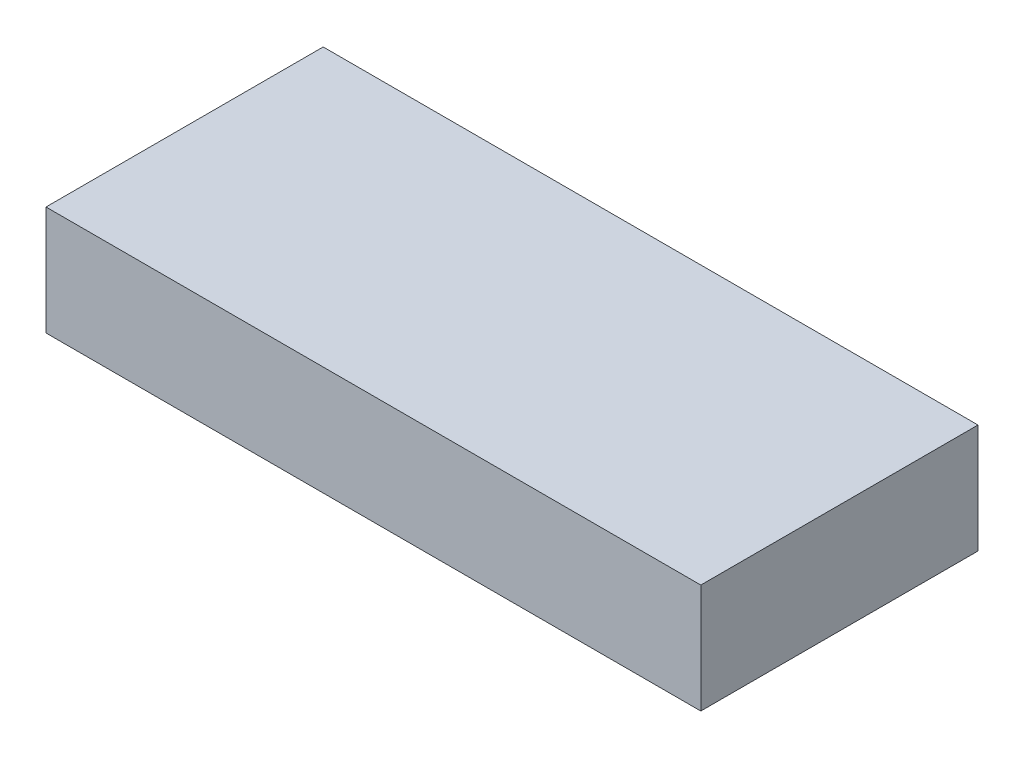
SolidWorks part; units mm, degrees
ref_plane "Front Plane" through (0, 0, 0) normal (0, 0, 1) x (1, 0, 0)
ref_plane "Top Plane" through (0, 0, 0) normal (0, 1, 0) x (1, 0, 0)
ref_plane "Right Plane" through (0, 0, 0) normal (1, 0, 0) x (0, 0, -1)
sketch "Sketch1" plane through (0, 0, 0) normal (0, 1, 0) x (1, 0, 0)
  line L1 (-30, -12.7) -> (30, -12.7)
  line L2 (-30, -12.7) -> (-30, 12.7)
  line L3 (-30, 12.7) -> (30, 12.7)
  line L4 (30, -12.7) -> (30, 12.7)
  line L5 (-30, -12.7) -> (30, 12.7) construction
  line L6 (-30, 12.7) -> (30, -12.7) construction
  point P0 (0, 0)
  dimension "D1" = 60
  dimension "D2" = 25.4
extrude "Boss-Extrude1" add sketch "Sketch1" along normal mid plane 10
